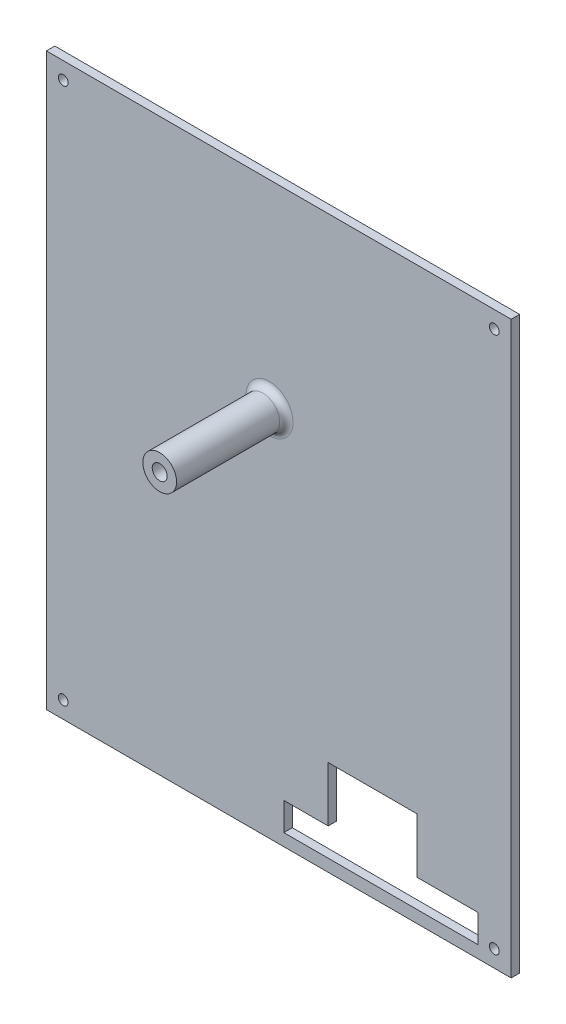
SolidWorks part; units mm, degrees
ref_plane "Front Plane" through (0, 0, 0) normal (0, 0, 1) x (1, 0, 0)
ref_plane "Top Plane" through (0, 0, 0) normal (0, 1, 0) x (1, 0, 0)
ref_plane "Right Plane" through (0, 0, 0) normal (1, 0, 0) x (0, 0, -1)
sketch "Sketch1" plane through (0, 0, 0) normal (0, 0, 1) x (1, 0, 0)
  line L1 (0, 0) -> (-139.7, 0)
  line L2 (0, 0) -> (0, 171.45)
  line L3 (0, 171.45) -> (-139.7, 171.45)
  line L4 (-139.7, 0) -> (-139.7, 171.45)
  dimension "6.7" = 171.45
  dimension "D2" = 139.7
extrude "Boss-Extrude1" add sketch "Sketch1" along normal blind 2.54
sketch "Sketch2" plane through (0, 0, 2.54) normal (0, 0, 1) x (1, 0, 0)
  line L0 (-139.7, 0) -> (0, 0) construction
  line L9 (-129.54, 83.566) -> (-71.628, 83.566) construction
  line L10 (-129.54, 83.566) -> (-129.54, 3.81) construction
  line L11 (-129.54, 3.81) -> (-71.628, 3.81) construction
  line L12 (-71.628, 83.566) -> (-71.628, 3.81) construction
  line L13 (-68.072, 83.566) -> (-10.16, 83.566) construction
  line L14 (-68.072, 83.566) -> (-68.072, 3.81) construction
  line L15 (-68.072, 3.81) -> (-10.16, 3.81) construction
  line L16 (-10.16, 83.566) -> (-10.16, 3.81) construction
  line L17 (0, 0) -> (0, 171.45) construction
  line L18 (-139.7, 171.45) -> (-139.7, 0) construction
  line L19 (-39.116, 83.566) -> (-39.116, 78.3316) construction
  line L20 (-121.7061, 111.8489) -> (-115.1316, 87.3125)
  line L21 (-115.1316, 87.3125) -> (-97.1697, 69.3506)
  line L22 (-97.1697, 69.3506) -> (-72.6333, 62.7761)
  line L23 (-72.6333, 62.7761) -> (-48.0969, 69.3506)
  line L24 (-48.0969, 69.3506) -> (-30.1351, 87.3125)
  line L25 (-30.1351, 87.3125) -> (-23.5605, 111.8489)
  line L26 (-23.5605, 111.8489) -> (-30.1351, 136.3853)
  line L27 (-30.1351, 136.3853) -> (-48.0969, 154.3472)
  line L28 (-48.0969, 154.3472) -> (-72.6333, 160.9217)
  line L29 (-72.6333, 160.9217) -> (-97.1697, 154.3472)
  line L30 (-97.1697, 154.3472) -> (-115.1316, 136.3853)
  line L31 (-115.1316, 136.3853) -> (-121.7061, 111.8489)
  line L32 (-39.116, 78.3316) -> (83.9241, 78.3316) construction
  line L33 (-39.116, 78.3316) -> (74.2286, 12.892) construction
  line L34 (-39.116, 78.3316) -> (35.1071, 121.1843) construction
  line L35 (-31.6039, 11.938) -> (-10.16, 11.938) construction
  line L36 (-68.072, 3.81) -> (-10.16, 3.81) construction
  line L37 (-68.072, 3.81) -> (-68.072, 11.938) construction
  line L38 (-68.072, 11.938) -> (-46.628, 11.938) construction
  line L39 (-10.16, 3.81) -> (-10.16, 11.938) construction
  line L41 (-46.628, 11.938) -> (-46.628, 28.0289) construction
  line L42 (-46.628, 28.0289) -> (-31.604, 28.0289) construction
  line L43 (-31.6039, 11.938) -> (-31.604, 28.0289) construction
  line L44 (-39.116, 28.0289) -> (-39.116, 78.3316) construction
  circle A1 centre (-72.6333, 111.8489) radius 47.4007 construction
  point P17 (-39.116, 78.3316)
  point P41 (-39.116, 28.0289)
  point P42 (-39.116, 3.81)
  dimension "D9" = 45
  dimension "D10" = 98.1456
  dimension "D1" = 79.756
  dimension "D2" = 79.756
  dimension "D3" = 57.912
  dimension "D4" = 57.912
  dimension "D5" = 3.81
  dimension "D6" = 10.16
  dimension "D7" = 3.81
  dimension "D8" = 10.16
  dimension "D11" = 30
  dimension "D12" = 30
  dimension "D13" = 8.128
  dimension "D14" = 16.0909
  dimension "D15" = 15.0241
  dimension "D16" = 83.82
  dimension "D17" = 33.5173
sketch "Sketch3" plane through (0, 0, 2.54) normal (0, 0, 1) x (1, 0, 0)
  line L0 (-28.321, 12.065) -> (-9.906, 12.065)
  line L1 (-68.326, 12.065) -> (-54.991, 12.065)
  line L2 (-68.326, 12.065) -> (-68.326, 3.683)
  line L3 (-68.326, 3.683) -> (-9.906, 3.683)
  line L4 (-9.906, 12.065) -> (-9.906, 3.683)
  line L7 (-49.911, 28.575) -> (-28.321, 28.575)
  line L8 (-28.321, 12.065) -> (-28.321, 28.575)
  line L9 (-139.7, 0) -> (0, 0) construction
  line L10 (0, 0) -> (0, 171.45) construction
  line L11 (-49.911, 28.575) -> (-54.991, 28.575)
  line L12 (-54.991, 28.575) -> (-54.991, 12.065)
  point P12 (-39.116, 28.575)
  point P13 (-39.116, 3.683)
  dimension "D1" = 8.382
  dimension "D2" = 3.683
  dimension "D3" = 58.42
  dimension "D4" = 9.906
  dimension "D5" = 21.59
  dimension "D6" = 16.51
  dimension "D7" = 5.08
extrude "Cut-Extrude1" cut sketch "Sketch3" against normal blind 2.54
sketch "Sketch4" plane through (0, 0, 2.54) normal (0, 0, 1) x (1, 0, 0)
  circle A0 centre (-72.6333, 111.8489) radius 12.954
  dimension "D1" = 25.908
extrude "Cut-Extrude2" [suppressed] cut sketch "Sketch4" against normal through all
sketch "Sketch5" plane through (0, 0, 0) normal (0, 0, -1) x (-1, 0, 0)
  circle A1 centre (72.6333, 111.8489) radius 14.478
  dimension "D2" = 28.956
extrude "Boss-Extrude2" [suppressed] add sketch "Sketch5" along normal blind 7.62 separate body
sketch "Sketch6" [suppressed] plane through (0, 0, 0) normal (0, 0, 1) x (1, 0, 0)
  circle A0 centre (-72.6333, 111.8489) radius 12.954
  dimension "D1" = 25.908
extrude "Cut-Extrude3" [suppressed] cut sketch "Sketch6" against normal blind 5.08
sketch "Sketch7" [suppressed] plane through (0, 0, -5.08) normal (0, 0, 1) x (1, 0, 0)
  circle A0 centre (-72.6333, 111.8489) radius 5.2705
  dimension "D1" = 10.541
extrude "Cut-Extrude4" [suppressed] cut sketch "Sketch7" against normal blind 6.35
sketch "Sketch8" [suppressed] plane through (0, 0, -7.62) normal (0, 0, -1) x (-1, 0, 0)
  line L0 (111.8903, 123.6736) -> (91.8255, 80.637) construction
  line L1 (139.7, 0) -> (0, 0) construction
  line L2 (139.7, 171.45) -> (139.7, 0) construction
  line L4 (72.6333, 111.8489) -> (94.488, 104.394) construction
  circle A0 centre (94.488, 104.394) radius 8.89
  circle A1 centre (94.488, 104.394) radius 4.725
  circle A5 centre (101.8579, 102.1553) radius 14
  circle A6 centre (109.2527, 118.0162) radius 3
  circle A7 centre (94.4631, 86.2945) radius 3
  point P9 (94.488, 104.394)
  point P11 (101.8579, 102.1553)
  point P17 (90.1015, 106.1502)
  point P19 (88.5258, 106.4278)
  point P21 (110.5204, 120.7352)
  point P22 (93.1954, 83.5755)
  dimension "D1" = 17.78
  dimension "D2" = 104.394
  dimension "D3" = 45.212
  dimension "D4" = 9.45
  dimension "D5" = 6
  dimension "D6" = 6
  dimension "D7" = 28
  dimension "D8" = 1.6
  dimension "D9" = 20.5
  dimension "D10" = 20.5
sketch "Sketch9" [suppressed] plane through (0, 0, -7.62) normal (0, 0, -1) x (-1, 0, 0)
  line L1 (84.0779, 81.2145) -> (118.3679, 81.2145)
  line L2 (84.0779, 81.2145) -> (84.0779, 123.0962)
  line L3 (84.0779, 123.0962) -> (118.3679, 123.0962)
  line L4 (118.3679, 81.2145) -> (118.3679, 123.0962)
  circle A0 centre (94.4631, 86.2945) radius 3 construction
  circle A1 centre (109.2527, 118.0162) radius 3 construction
  circle A2 centre (101.8579, 102.1553) radius 14 construction
  dimension "D1" = 5.08
  dimension "D2" = 5.08
  dimension "D3" = 16.51
  dimension "D4" = 17.78
extrude "Boss-Extrude3" [suppressed] add sketch "Sketch9" against normal up to next
sketch "Sketch10" [suppressed] plane through (0, 0, -7.62) normal (0, 0, -1) x (-1, 0, 0)
  line L0 (118.3679, 108.1875) -> (113.0339, 108.1875)
  line L12 (103.6586, 81.2145) -> (103.6586, 89.5836)
  line L13 (118.3679, 123.0962) -> (100.7044, 123.0962)
  line L16 (100.7044, 123.0962) -> (100.7044, 114.8029)
  line L17 (84.0779, 92.8118) -> (93.2563, 92.8118)
  circle A0 centre (109.2527, 118.0162) radius 3.048
  circle A1 centre (94.4631, 86.2945) radius 3.048
  arc A2 (113.0339, 108.1875) -> (100.7044, 114.8029) centre (101.8579, 102.1553) ccw
  arc A6 (93.2563, 92.8118) -> (103.6586, 89.5836) centre (101.8579, 102.1553) ccw
  dimension "D1" = 6.096
  dimension "D2" = 6.096
  dimension "D5" = 12.7
extrude "Boss-Extrude4" [suppressed] add sketch "Sketch10" along normal blind 17.78
sketch "Sketch12" plane through (0, 0, 2.54) normal (0, 0, 1) x (1, 0, 0)
  line L0 (-139.7, 85.725) -> (-132.5025, 85.725) construction
  line L1 (-139.7, 171.45) -> (-139.7, 0) construction
  line L2 (-69.85, 171.45) -> (-69.85, 153.7893) construction
  line L3 (0, 171.45) -> (-139.7, 171.45) construction
  line L4 (-139.7, 0) -> (0, 0) construction
  circle A0 centre (-134.62, 5.08) radius 1.4668
  circle A2 centre (-134.62, 166.37) radius 1.4668
  circle A3 centre (-5.08, 166.37) radius 1.4668
  circle A4 centre (-5.08, 5.08) radius 1.4668
  dimension "D1" = 2.9337
  dimension "D3" = 5.08
  dimension "D2" = 5.08
extrude "Cut-Extrude6" cut sketch "Sketch12" against normal through all
sketch "Sketch14" plane through (0, 0, 2.54) normal (0, 0, 1) x (1, 0, 0)
  circle A0 centre (-134.62, 5.08) radius 3.6449
  dimension "D1" = 7.2898
extrude "Cut-Extrude8" [suppressed] cut sketch "Sketch14" against normal blind 0.508
sketch "Sketch15" [suppressed] plane through (0, 0, 2.54) normal (0, 0, 1) x (1, 0, 0)
  circle A0 centre (-77.8032, 111.8489) radius 12.954 construction
  circle A1 centre (-77.8032, 111.8489) radius 12.954
  arc A2 (-84.0779, 98.8013) -> (-86.9197, 123.0962) centre (-77.8032, 111.8489) ccw construction
  arc A3 (-84.0779, 98.8013) -> (-86.9197, 123.0962) centre (-77.8032, 111.8489) ccw
  circle A4 centre (-77.8032, 111.8489) radius 14.478
extrude "Cut-Extrude9" [suppressed] cut sketch "Sketch15" against normal through all
sketch "Sketch16" [suppressed] plane through (0, 0, 2.032) normal (0, 0, 1) x (1, 0, 0)
  circle A0 centre (-134.62, 5.08) radius 10.5205
extrude "Cut-Extrude10" [suppressed] cut sketch "Sketch16" against normal through all
sketch "Sketch17" plane through (0, 0, 2.54) normal (0, 0, 1) x (1, 0, 0)
  line L0 (-129.0157, 111.8489) -> (-16.251, 111.8489) construction
  line L1 (-24.4339, 157.6075) -> (-120.8328, 66.0903) construction
  line L2 (-109.1979, 60.334) -> (-125.9434, 78.0229)
  line L3 (-109.1979, 60.334) -> (-115.7222, 54.1576)
  line L4 (-125.9434, 78.0229) -> (-132.4677, 71.8466)
  line L5 (-115.7222, 54.1576) -> (-132.4677, 71.8466)
  line L6 (-109.1979, 60.334) -> (-132.4677, 71.8466) construction
  line L7 (-125.9434, 78.0229) -> (-115.7222, 54.1576) construction
  line L8 (-13.2398, 151.6806) -> (-29.739, 169.1094)
  line L9 (-13.2398, 151.6806) -> (-19.1287, 146.1057)
  line L10 (-29.739, 169.1094) -> (-35.628, 163.5345)
  line L11 (-19.1287, 146.1057) -> (-35.628, 163.5345)
  line L12 (-13.2398, 151.6806) -> (-35.628, 163.5345) construction
  line L13 (-29.739, 169.1094) -> (-19.1287, 146.1057) construction
  line L14 (-109.6434, 163.4873) -> (-126.1848, 146.0985)
  line L15 (-132.0603, 151.6876) -> (-126.1848, 146.0985)
  line L16 (-115.5189, 169.0764) -> (-132.0603, 151.6876)
  line L17 (-115.5189, 169.0764) -> (-109.6434, 163.4873)
  point P5 (-72.6333, 111.8489)
  point P6 (-72.6333, 111.8489)
  point P21 (-72.6333, 111.8489)
  dimension "D1" = 2
extrude "Boss-Extrude5" [suppressed] add sketch "Sketch17" along normal blind 35.56
sketch "Sketch18" [suppressed] plane through (0, 0, 38.1) normal (0, 0, 1) x (1, 0, 0)
  line L0 (-13.2398, 151.6806) -> (-29.739, 169.1094)
  line L1 (-13.2398, 151.6806) -> (-57.925, 109.3729)
  line L2 (-29.739, 169.1094) -> (-75.3393, 125.9354)
  line L3 (-115.9685, 54.4178) -> (-132.4677, 71.8466)
  line L4 (-132.0603, 151.6876) -> (-115.5189, 169.0764)
  line L5 (-132.0603, 151.6876) -> (-92.7356, 109.4646)
  line L6 (-115.5189, 169.0764) -> (-75.3393, 125.9354)
  line L8 (-92.7356, 109.4646) -> (-132.4677, 71.8466)
  line L9 (-70.9644, 97.0273) -> (-115.9685, 54.4178)
  arc A3 (-70.9644, 97.0273) -> (-57.925, 109.3729) centre (-72.6333, 111.8489) ccw
  circle A4 centre (-72.6333, 111.8489) radius 5.2705
extrude "Boss-Extrude6" [suppressed] add sketch "Sketch18" along normal blind 6.604
sketch "Sketch19" [suppressed] plane through (0, 0, 44.704) normal (0, 0, 1) x (1, 0, 0)
  circle A0 centre (-72.6333, 111.8489) radius 12.954
  dimension "D1" = 25.908
extrude "Cut-Extrude11" [suppressed] cut sketch "Sketch19" against normal blind 5.08
sketch "Sketch20" plane through (0, 0, 2.54) normal (0, 0, 1) x (1, 0, 0)
  circle A0 centre (-72.6333, 111.8489) radius 12.954
  circle A1 centre (-72.6333, 111.8489) radius 15.24
  dimension "D1" = 25.908
  dimension "D2" = 30.48
extrude "Boss-Extrude7" [suppressed] add sketch "Sketch20" along normal blind 4.826
sketch "Sketch21" [suppressed] plane through (0, 0, 39.624) normal (0, 0, 1) x (1, 0, 0)
  circle A0 centre (-72.6333, 111.8489) radius 5.2705
extrude "Cut-Extrude12" [suppressed] cut sketch "Sketch21" against normal through all
fillet "Fillet1" [suppressed] radius 2.54
sketch "Sketch22" plane through (0, 0, 2.54) normal (0, 0, 1) x (1, 0, 0)
  circle A0 centre (-72.6333, 111.8489) radius 12.954
extrude "Cut-Extrude13" [suppressed] cut sketch "Sketch22" against normal blind 1.27
sketch "Sketch23" plane through (0, 0, 2.54) normal (0, 0, 1) x (1, 0, 0)
  circle A0 centre (-72.6333, 111.8489) radius 12.954
  dimension "D1" = 25.908
extrude "Cut-Extrude14" [suppressed] cut sketch "Sketch23" against normal blind 2.54
sketch "Sketch24" plane through (0, 0, 2.54) normal (0, 0, 1) x (1, 0, 0)
  circle A0 centre (-72.6333, 111.8489) radius 5.075
  dimension "D1" = 10.15
extrude "Boss-Extrude8" add sketch "Sketch24" along normal blind 33
sketch "Sketch25" plane through (0, 0, 2.54) normal (0, 0, 1) x (1, 0, 0)
  circle A0 centre (-72.6333, 111.8489) radius 10
  dimension "D1" = 20
fillet "Fillet2" radius 2 1 edges at (-67.5583, 111.8489, 2.54)
sketch "Sketch26" plane through (0, 0, 35.54) normal (0, 0, 1) x (1, 0, 0)
  circle A0 centre (-72.6333, 111.8489) radius 2.25
  dimension "D1" = 4.5
extrude "Cut-Extrude16" cut sketch "Sketch26" against normal blind 5
